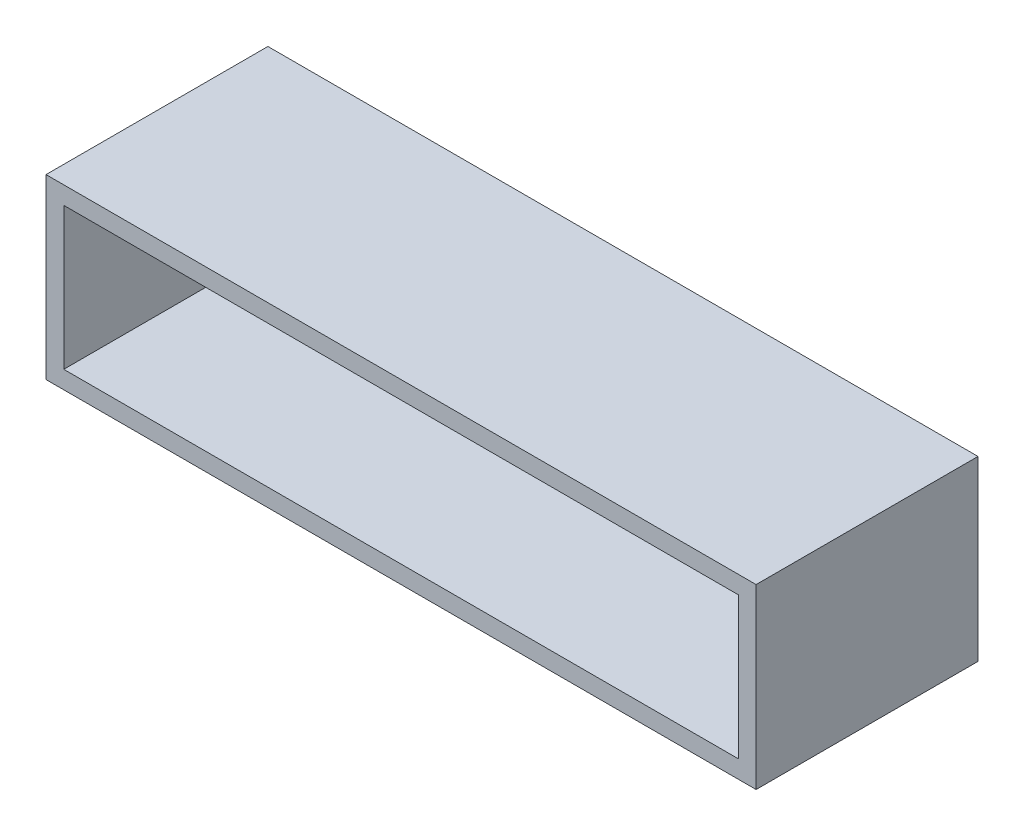
SolidWorks part; units mm, degrees
ref_plane "Front Plane" through (0, 0, 0) normal (0, 0, 1) x (1, 0, 0)
ref_plane "Top Plane" through (0, 0, 0) normal (0, 1, 0) x (1, 0, 0)
ref_plane "Right Plane" through (0, 0, 0) normal (1, 0, 0) x (0, 0, -1)
sketch "Sketch1" plane through (0, 0, 0) normal (0, 1, 0) x (1, 0, 0)
  line L1 (-44.1966, -30.0782) -> (35.8034, -30.0782)
  line L2 (-44.1966, -30.0782) -> (-44.1966, -5.0782)
  line L3 (-44.1966, -5.0782) -> (35.8034, -5.0782)
  line L4 (35.8034, -30.0782) -> (35.8034, -5.0782)
extrude "Boss-Extrude1" add sketch "Sketch1" along normal blind 20
sketch "Sketch3" plane through (0, 0, 30.0782) normal (0, 0, 1) x (1, 0, 0)
  line L9 (-42.1966, 18) -> (33.8034, 18)
  line L10 (-42.1966, 18) -> (-42.1966, 2)
  line L11 (-42.1966, 2) -> (33.8034, 2)
  line L12 (33.8034, 18) -> (33.8034, 2)
extrude "Cut-Extrude1" cut sketch "Sketch3" against normal blind 23
sketch "Sketch4" plane through (0, 0, 7.0782) normal (0, 0, 1) x (1, 0, 0)
  circle A0 centre (30.8034, 10) radius 1
  circle A1 centre (-39.1966, 10) radius 1
extrude "Cut-Extrude2" cut sketch "Sketch4" against normal blind 48
sketch "Sketch5" plane through (0, 0, 7.0782) normal (0, 0, 1) x (1, 0, 0)
  circle A0 centre (-31.6966, 10) radius 2.5
  circle A1 centre (23.3034, 10) radius 2.5
extrude "Cut-Extrude3" cut sketch "Sketch5" against normal blind 48
